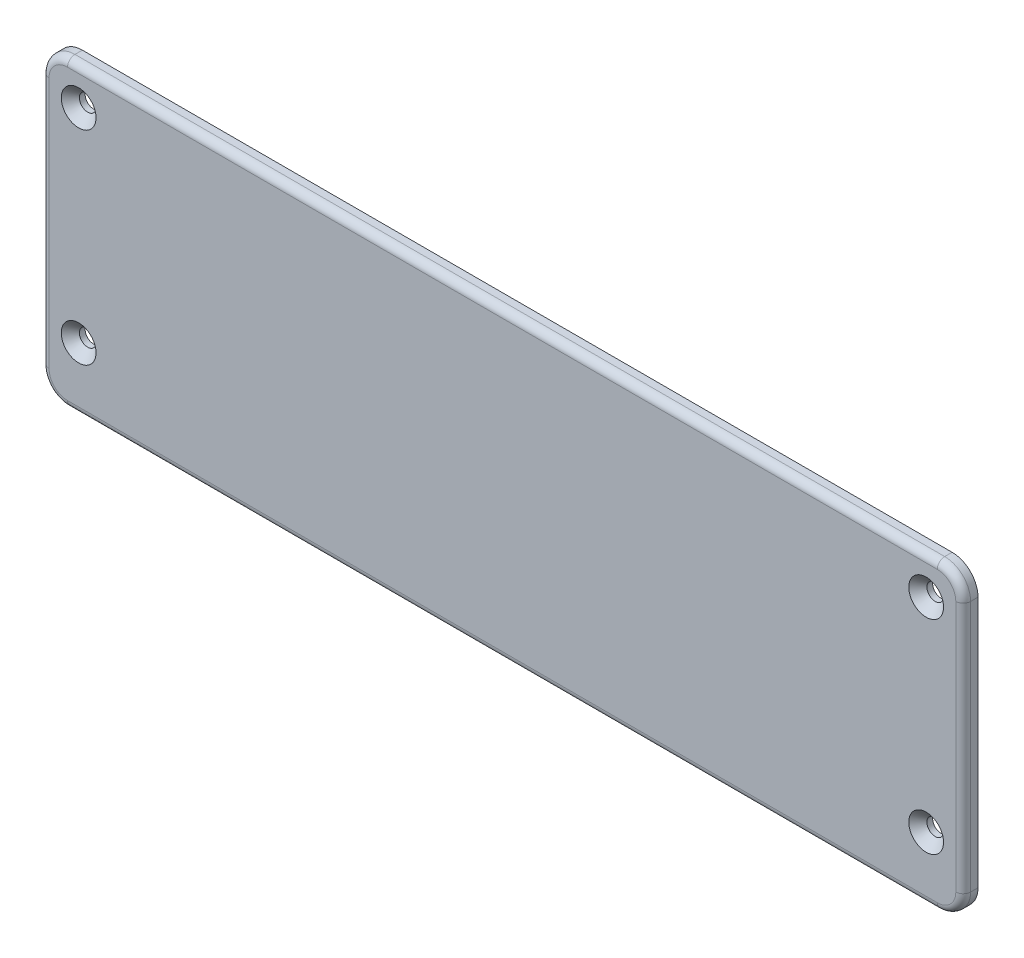
SolidWorks part; units mm, degrees
ref_plane "Plan de face" through (0, 0, 0) normal (0, 0, 1) x (1, 0, 0)
ref_plane "Plan de dessus" through (0, 0, 0) normal (0, 1, 0) x (1, 0, 0)
ref_plane "Plan de droite" through (0, 0, 0) normal (1, 0, 0) x (0, 0, -1)
sketch "Esquisse1" plane through (0, 0, 0) normal (0, 0, 1) x (1, 0, 0)
  line L0 (-124.5, 41) -> (-124.5, -41)
  line L1 (-124.5, -41) -> (124.5, -41)
  line L2 (0, -2.2) -> (0, 2.2) construction
  line L3 (124.5, 41) -> (124.5, -41)
  line L4 (2.2, 0) -> (-2.2, 0) construction
  line L5 (-124.5, 41) -> (124.5, 41)
  dimension "D1" = 82
  dimension "D2" = 249
extrude "Boss.-Extru.1" add sketch "Esquisse1" along normal blind 4
sketch "Esquisse2" plane through (0, 0, 4) normal (0, 0, 1) x (1, 0, 0)
  line L0 (-114.5, 41) -> (-114.5, 31) construction
  line L1 (124.5, 41) -> (-124.5, 41) construction
  line L2 (-114.5, 31) -> (-124.5, 31) construction
  line L3 (-124.5, 41) -> (-124.5, -41) construction
  line L4 (-124.5, -24) -> (-114.5, -24) construction
  line L5 (-114.5, -24) -> (-114.5, -41) construction
  line L6 (-124.5, -41) -> (124.5, -41) construction
  line L8 (0, -2.2) -> (0, 2.2) construction
  point P1 (-114.5, 31)
  point P8 (-114.5, -24)
  point P15 (114.5, -24)
  point P16 (114.5, 31)
  point P19 (-114.5, 31)
  point P22 (-114.5, -24)
  dimension "D1" = 10
  dimension "D2" = 10
  dimension "D3" = 17
hole_wizard "Fraisage pour vis à tête fraisée M42" positions "Esquisse2" profile "Esquisse6" countersink size "M4" standard "Ansi Metric" end condition through all
sketch "Esquisse6" plane through (-114.5, -24, 4) normal (1, 0, 0) x (0, -1, 0)
  line L0 (0, 0) -> (0, 4)
  line L1 (0, 4) -> (2.25, 4)
  line L2 (2.25, 4) -> (2.25, 2.45)
  line L3 (2.25, 2.45) -> (4.7, 0)
  line L5 (4.7, 0) -> (0, 0)
  line L6 (-2.25, 2.45) -> (-4.7, 0) construction
  line L11 (0, -6.35) -> (0, 107.95) construction
  dimension "Diamètre du perçage jusqu'au prochain" = 4.5
  dimension "Profondeur du perçage jusqu'au prochain" = 4
  dimension "Diamètre du fraisage entrant" = 9.4
  dimension "Angle du fraisage entrant" = 90
fillet "Congé1" radius 7 4 edges at (124.5, 41, 2) (124.5, -41, 2) (-124.5, -41, 2) (-124.5, 41, 2)
fillet "Congé2" radius 2 8 edges at (-122.4497, -38.9497, 4) (-124.5, 0, 4) (-122.4497, 38.9497, 4) (0, 41, 4) (122.4497, 38.9497, 4) (124.5, 0, 4) (122.4497, -38.9497, 4) (0, -41, 4)
